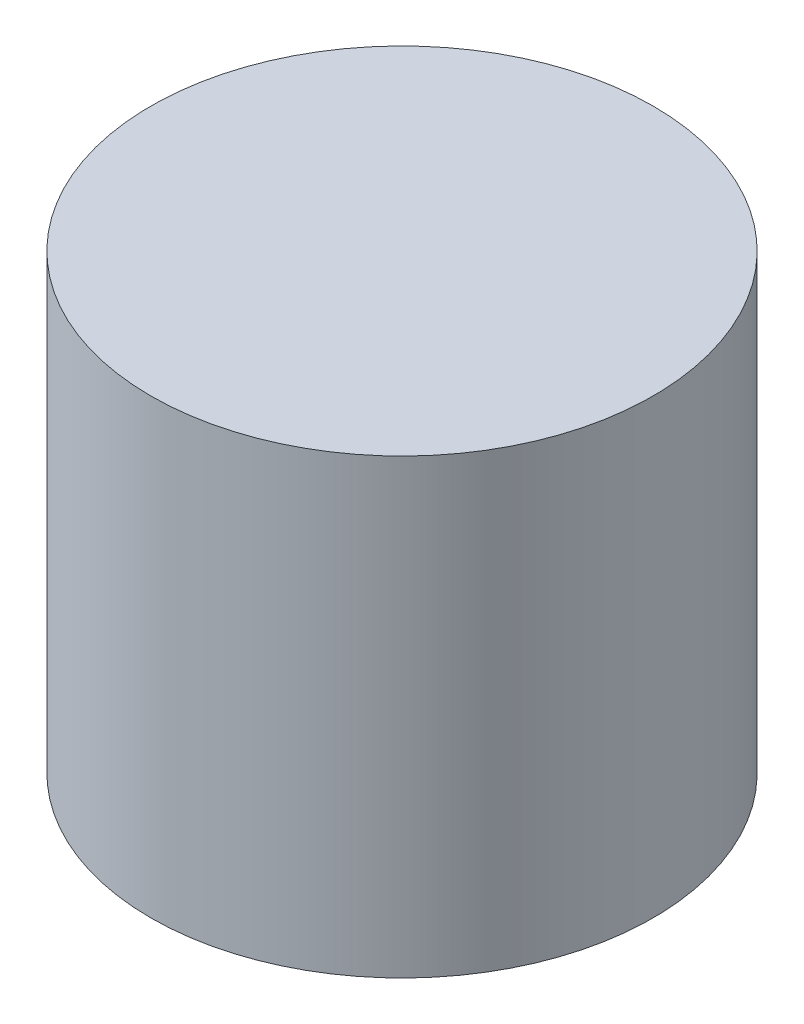
SolidWorks part; units mm, degrees
ref_plane "Front Plane" through (0, 0, 0) normal (0, 0, 1) x (1, 0, 0)
ref_plane "Top Plane" through (0, 0, 0) normal (0, 1, 0) x (1, 0, 0)
ref_plane "Right Plane" through (0, 0, 0) normal (1, 0, 0) x (0, 0, -1)
sketch "Sketch1" plane through (0, 0, 0) normal (0, 1, 0) x (1, 0, 0)
  circle A0 centre (0, 0) radius 5
extrude "Boss-Extrude1" add sketch "Sketch1" along normal blind 9 contours A0
